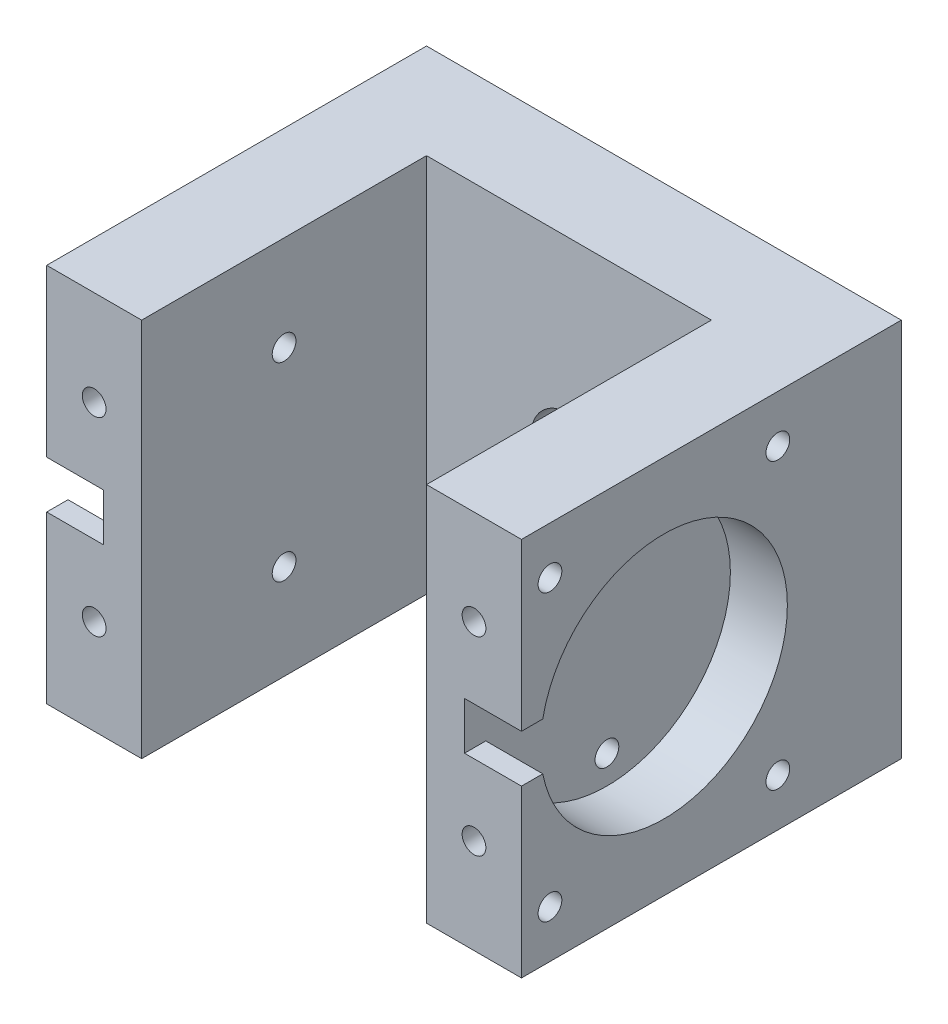
SolidWorks part; units mm, degrees
ref_plane "Front" through (0, 0, 0) normal (0, 0, 1) x (1, 0, 0)
ref_plane "Top" through (0, 0, 0) normal (0, 1, 0) x (1, 0, 0)
ref_plane "Right" through (0, 0, 0) normal (1, 0, 0) x (0, 0, -1)
sketch "Sketch1" plane through (0, 0, 0) normal (0, 1, 0) x (1, 0, 0)
  line L1 (25, -20) -> (-25, -20)
  line L2 (25, -20) -> (25, 20)
  line L3 (25, 20) -> (-25, 20)
  line L4 (-25, -20) -> (-25, 20)
  line L5 (25, -20) -> (-25, 20) construction
  line L6 (25, 20) -> (-25, -20) construction
  point P0 (0, 0)
  dimension "D1" = 50
  dimension "D2" = 40
extrude "Boss-Extrude1" add sketch "Sketch1" along normal blind 40
sketch "Sketch2" plane through (0, 40, 0) normal (0, 1, 0) x (1, 0, 0)
  line L0 (-25, -20) -> (25, -20) construction
  line L1 (-15, -20) -> (15, -20)
  line L2 (-15, -20) -> (-15, 10)
  line L3 (-15, 10) -> (15, 10)
  line L4 (15, -20) -> (15, 10)
  line L5 (-25, 20) -> (-25, -20) construction
  dimension "D1" = 30
  dimension "D2" = 30
  dimension "D3" = 10
extrude "Cut-Extrude1" cut sketch "Sketch2" against normal up to next
sketch "Sketch3" plane through (-25, 0, 0) normal (-1, 0, 0) x (0, 0, 1)
  line L1 (-20, 40) -> (-20, 0) construction
  line L2 (-20, 0) -> (20, 0) construction
  circle A0 centre (5, 20) radius 13
  dimension "D1" = 26
  dimension "D2" = 25
  dimension "D3" = 20
extrude "Cut-Extrude2" cut sketch "Sketch3" against normal blind 6
sketch "Sketch4" plane through (25, 0, 0) normal (1, 0, 0) x (0, 0, -1)
  line L0 (-20, 40) -> (20, 40) construction
  line L1 (20, 40) -> (20, 0) construction
  circle A0 centre (-5, 20) radius 13
  circle A1 centre (-5, 20) radius 10 construction
  dimension "D1" = 26
  dimension "D4" = 20
  dimension "D2" = 20
  dimension "D3" = 25
extrude "Cut-Extrude3" cut sketch "Sketch4" against normal blind 6
hole_wizard "M3x0.5 Tapped Hole1" positions "Sketch8" profile "Sketch7" tap size "M3x0.5" standard "Ansi Metric"
sketch "Sketch8" plane through (-19, 0, 0) normal (-1, 0, 0) x (0, 0, 1)
  line L1 (20, 40) -> (20, 0) construction
  line L2 (-20, 40) -> (20, 40) construction
  line L3 (-20, 0) -> (20, 0) construction
  point P0 (5, 30)
  point P1 (5, 10)
  dimension "D1" = 15
  dimension "D2" = 10
  dimension "D3" = 15
  dimension "D4" = 10
sketch "Sketch7" plane through (-19, 30, 5) normal (0, 1, 0) x (0, 0, 1)
  line L0 (0, 0) -> (0, 7.2511)
  line L1 (0, 7.2511) -> (1.25, 6.5)
  line L2 (1.25, 6.5) -> (1.25, 0)
  line L5 (1.25, 0) -> (0, 0)
  line L10 (0, 7.2511) -> (-1.25, 6.5) construction
  line L11 (0, -6.35) -> (0, 107.95) construction
  dimension "Tap Drill Dia." = 2.5
  dimension "Tap Drill Depth" = 6.5
  dimension "Drill Angle" = 118
cosmetic thread "Hole Thread1" parameters "D1"=4, "D2"=3
cosmetic thread "Hole Thread2" parameters "D1"=4, "D2"=3
hole_wizard "M3x0.5 Tapped Hole2" positions "Sketch10" profile "Sketch9" tap size "M3x0.5" standard "Ansi Metric"
sketch "Sketch10" plane through (19, 0, 0) normal (1, 0, 0) x (0, 0, -1)
  line L1 (-20, 40) -> (-20, 0) construction
  line L2 (-20, 0) -> (20, 0) construction
  line L3 (-20, 40) -> (20, 40) construction
  point P0 (-5, 30)
  point P1 (-5, 10)
  dimension "D1" = 15
  dimension "D2" = 10
  dimension "D3" = 15
  dimension "D4" = 10
sketch "Sketch9" plane through (19, 30, 5) normal (0, 1, 0) x (0, 0, -1)
  line L0 (0, 0) -> (0, 7.2511)
  line L1 (0, 7.2511) -> (1.25, 6.5)
  line L2 (1.25, 6.5) -> (1.25, 0)
  line L5 (1.25, 0) -> (0, 0)
  line L10 (0, 7.2511) -> (-1.25, 6.5) construction
  line L11 (0, -6.35) -> (0, 107.95) construction
  dimension "Tap Drill Dia." = 2.5
  dimension "Tap Drill Depth" = 6.5
  dimension "Drill Angle" = 118
cosmetic thread "Hole Thread3" parameters "D1"=4, "D2"=3
cosmetic thread "Hole Thread4" parameters "D1"=4, "D2"=3
hole_wizard "M3x0.5 Tapped Hole3" positions "Sketch12" profile "Sketch11" tap size "M3x0.5" standard "Ansi Metric"
sketch "Sketch12" plane through (0, 0, 20) normal (0, 0, 1) x (1, 0, 0)
  line L0 (-25, 40) -> (-25, 0) construction
  line L1 (-25, 40) -> (-15, 40) construction
  line L2 (-25, 0) -> (-15, 0) construction
  line L3 (15, 40) -> (25, 40) construction
  line L4 (25, 40) -> (25, 0) construction
  line L5 (15, 0) -> (25, 0) construction
  point P0 (-20, 30)
  point P1 (-20, 10)
  point P3 (20, 10)
  point P5 (20, 30)
  dimension "D1" = 5
  dimension "D2" = 10
  dimension "D3" = 5
  dimension "D4" = 10
  dimension "D5" = 10
  dimension "D6" = 5
  dimension "D7" = 5
  dimension "D8" = 10
sketch "Sketch11" plane through (-20, 30, 20) normal (1, 0, 0) x (0, -1, 0)
  line L0 (0, 0) -> (0, 4.7511)
  line L1 (0, 4.7511) -> (1.25, 4)
  line L2 (1.25, 4) -> (1.25, 0)
  line L5 (1.25, 0) -> (0, 0)
  line L10 (0, 4.7511) -> (-1.25, 4) construction
  line L11 (0, -6.35) -> (0, 107.95) construction
  dimension "Tap Drill Dia." = 2.5
  dimension "Tap Drill Depth" = 4
  dimension "Drill Angle" = 118
cosmetic thread "Hole Thread5" parameters "D1"=4, "D2"=3
cosmetic thread "Hole Thread6" parameters "D1"=4, "D2"=3
cosmetic thread "Hole Thread7" parameters "D1"=4, "D2"=3
cosmetic thread "Hole Thread8" parameters "D1"=4, "D2"=3
sketch "Sketch13" plane through (0, 0, -10) normal (0, 0, 1) x (1, 0, 0)
  line L0 (15, 40) -> (-15, 40) construction
  line L1 (15, 0) -> (15, 40) construction
  circle A0 centre (0, 20) radius 4
  point P4 (15, 20)
  dimension "D3" = 8
  dimension "D1" = 20
  dimension "D2" = 15
extrude "Cut-Extrude4" cut sketch "Sketch13" against normal blind 8
sketch "Sketch15" plane through (25, 0, 0) normal (1, 0, 0) x (0, 0, -1)
  line L0 (-20, 40) -> (-20, 0) construction
  line L1 (-20, 22.5) -> (-16, 22.5)
  line L2 (-20, 22.5) -> (-20, 17.5)
  line L3 (-20, 17.5) -> (-16, 17.5)
  line L4 (-16, 22.5) -> (-16, 17.5)
  line L5 (-20, 40) -> (20, 40) construction
  dimension "D1" = 5
  dimension "D2" = 4
  dimension "D3" = 17.5
extrude "Cut-Extrude5" cut sketch "Sketch15" against normal blind 6
sketch "Sketch16" plane through (-25, 0, 0) normal (-1, 0, 0) x (0, 0, 1)
  line L1 (20, 22.5) -> (16, 22.5)
  line L2 (20, 22.5) -> (20, 17.5)
  line L3 (20, 17.5) -> (16, 17.5)
  line L4 (16, 22.5) -> (16, 17.5)
  dimension "D1" = 5
  dimension "D2" = 4
extrude "Cut-Extrude6" cut sketch "Sketch16" against normal blind 6
sketch "Sketch17" plane through (25, 0, 0) normal (1, 0, 0) x (0, 0, -1)
  circle A0 centre (-5, 20) radius 10 construction
  dimension "D1" = 20
sketch "Sketch18" plane through (-25, 0, 0) normal (-1, 0, 0) x (0, 0, 1)
  circle A0 centre (5, 20) radius 10 construction
  dimension "D1" = 20
hole_wizard "M3x0.5 Tapped Hole4" positions "Sketch20" profile "Sketch19" tap size "M3x0.5" standard "Ansi Metric"
sketch "Sketch20" plane through (-25, 0, 0) normal (-1, 0, 0) x (0, 0, 1)
  point P0 (-7, 35)
  point P1 (-7, 5)
  point P3 (17, 5)
  point P5 (17, 35)
  dimension "D1" = 12
  dimension "D2" = 15
  dimension "D3" = 15
  dimension "D4" = 12
  dimension "D5" = 12
  dimension "D6" = 15
  dimension "D7" = 15
  dimension "D8" = 12
sketch "Sketch19" plane through (-25, 35, -7) normal (0, 1, 0) x (0, 0, 1)
  line L0 (0, 0) -> (0, 7.2511)
  line L1 (0, 7.2511) -> (1.25, 6.5)
  line L2 (1.25, 6.5) -> (1.25, 0)
  line L5 (1.25, 0) -> (0, 0)
  line L10 (0, 7.2511) -> (-1.25, 6.5) construction
  line L11 (0, -6.35) -> (0, 107.95) construction
  dimension "Tap Drill Dia." = 2.5
  dimension "Tap Drill Depth" = 6.5
  dimension "Drill Angle" = 118
cosmetic thread "Hole Thread9" parameters "D1"=4, "D2"=3
cosmetic thread "Hole Thread10" parameters "D1"=4, "D2"=3
cosmetic thread "Hole Thread11" parameters "D1"=4, "D2"=3
cosmetic thread "Hole Thread12" parameters "D1"=4, "D2"=3
hole_wizard "M3x0.5 Tapped Hole5" positions "Sketch22" profile "Sketch21" tap size "M3x0.5" standard "Ansi Metric"
sketch "Sketch22" plane through (25, 0, 0) normal (1, 0, 0) x (0, 0, -1)
  point P0 (-17, 35)
  point P1 (7, 35)
  point P3 (7, 5)
  point P5 (-17, 5)
  dimension "D1" = 12
  dimension "D2" = 15
  dimension "D3" = 15
  dimension "D4" = 12
  dimension "D5" = 12
  dimension "D6" = 15
  dimension "D7" = 12
  dimension "D8" = 15
sketch "Sketch21" plane through (25, 35, 17) normal (0, 1, 0) x (0, 0, -1)
  line L0 (0, 0) -> (0, 7.2511)
  line L1 (0, 7.2511) -> (1.25, 6.5)
  line L2 (1.25, 6.5) -> (1.25, 0)
  line L5 (1.25, 0) -> (0, 0)
  line L10 (0, 7.2511) -> (-1.25, 6.5) construction
  line L11 (0, -6.35) -> (0, 107.95) construction
  dimension "Tap Drill Dia." = 2.5
  dimension "Tap Drill Depth" = 6.5
  dimension "Drill Angle" = 118
cosmetic thread "Hole Thread13" parameters "D1"=4, "D2"=3
cosmetic thread "Hole Thread14" parameters "D1"=4, "D2"=3
cosmetic thread "Hole Thread15" parameters "D1"=4, "D2"=3
cosmetic thread "Hole Thread16" parameters "D1"=4, "D2"=3
